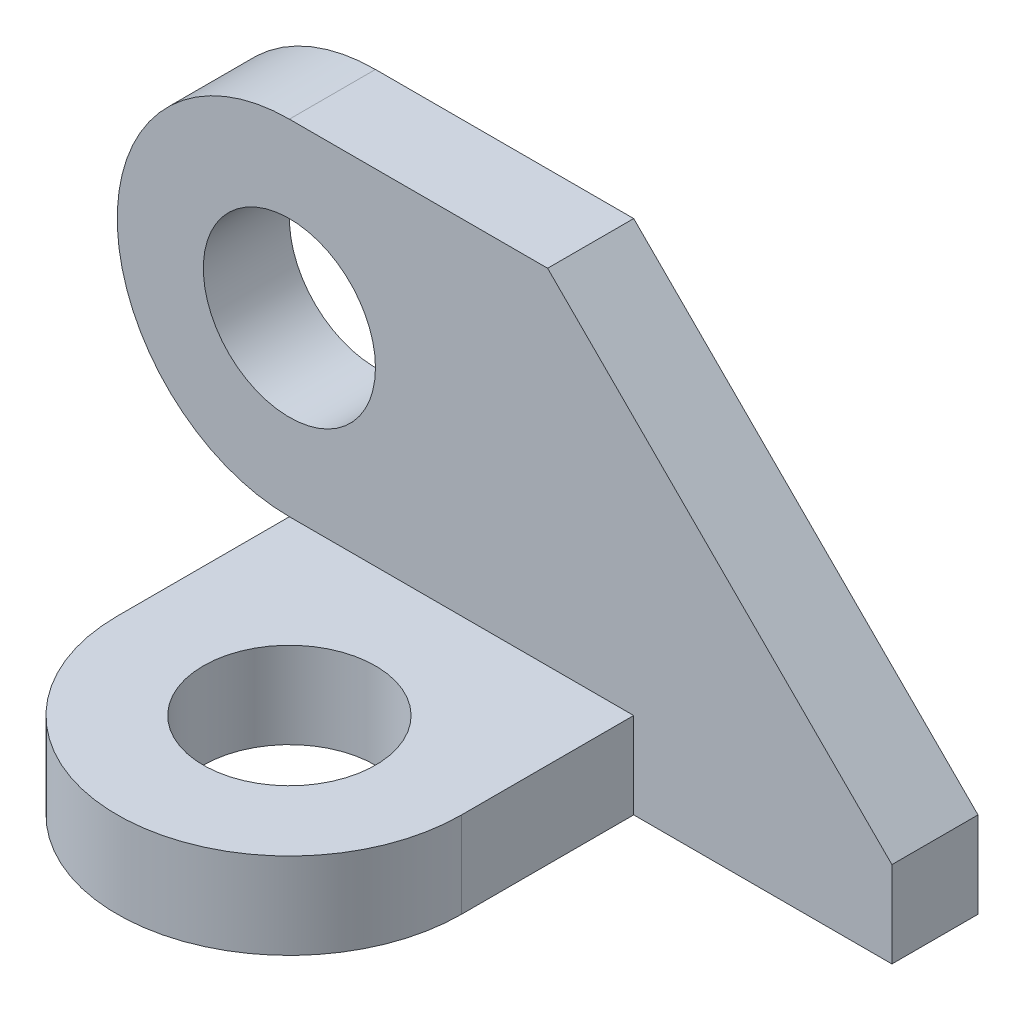
SolidWorks part; units mm, degrees
ref_plane "前基準面" through (0, 0, 0) normal (0, 0, 1) x (1, 0, 0)
ref_plane "上基準面" through (0, 0, 0) normal (0, 1, 0) x (1, 0, 0)
ref_plane "右基準面" through (0, 0, 0) normal (1, 0, 0) x (0, 0, -1)
sketch "草圖1" plane through (0, 0, 0) normal (0, 0, 1) x (1, 0, 0)
  line L0 (0, 10) -> (15, 10)
  line L1 (15, 10) -> (35, -10)
  line L2 (35, -10) -> (35, -15)
  line L3 (35, -15) -> (0, -15)
  line L4 (0, -15) -> (0, -10)
  circle A0 centre (0, 0) radius 5
  arc A1 (0, 10) -> (0, -10) centre (0, 0) ccw
  dimension "D1" = 10
  dimension "D2" = 20
  dimension "D3" = 15
  dimension "D4" = 5
  dimension "D5" = 35
  dimension "D6" = 5
extrude "填料-伸長1" add sketch "草圖1" along normal blind 5
sketch "草圖2" plane through (0, 0, 0) normal (0, 1, 0) x (1, 0, 0)
  line L0 (0, 0) -> (0, -15) construction
  line L1 (0, -15) -> (10, -15) construction
  line L2 (10, -15) -> (10, -12.0355) construction
  line L3 (0, -15) -> (0, -5)
  line L4 (20, -15) -> (20, -5)
  line L5 (35, -5) -> (15, -5) construction
  line L6 (20, -5) -> (0, -5)
  circle A0 centre (10, -15) radius 5
  arc A1 (0, -15) -> (20, -15) centre (10, -15) ccw
  dimension "D3" = 20
  dimension "D4" = 10
  dimension "D2" = 15
extrude "填料-伸長2" add sketch "草圖2" along normal blind 5 from surface at -15 starting at face at (17.5, -15, 2.5)
